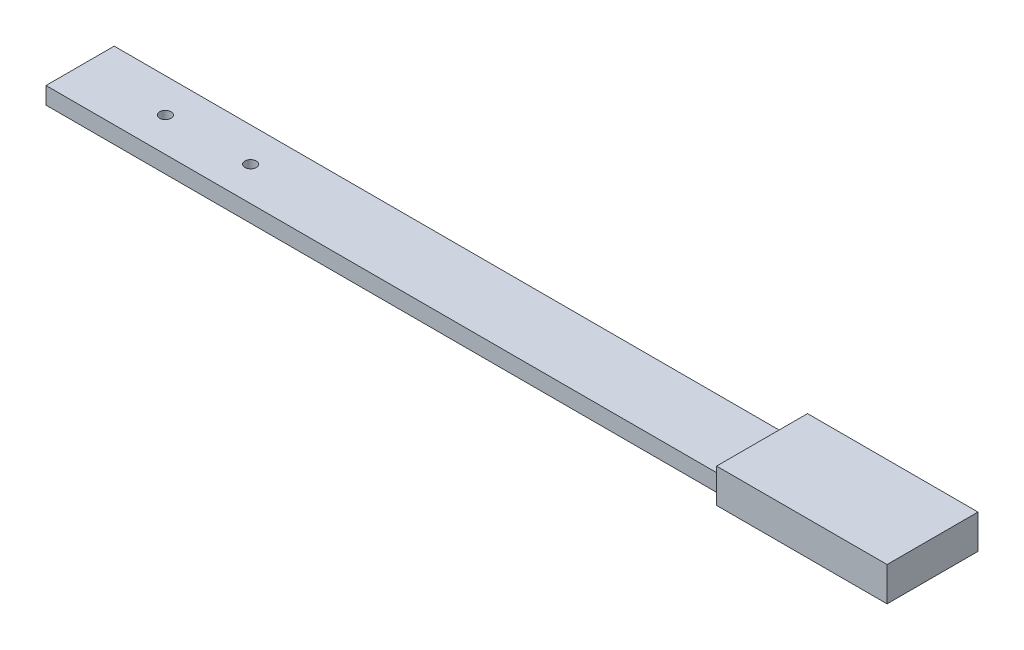
SolidWorks part; units mm, degrees
ref_plane "Ön Düzlem" through (0, 0, 0) normal (0, 0, 1) x (1, 0, 0)
ref_plane "Üst Düzlem" through (0, 0, 0) normal (0, 1, 0) x (1, 0, 0)
ref_plane "Sağ Düzlem" through (0, 0, 0) normal (1, 0, 0) x (0, 0, -1)
sketch "Çizim1" plane through (0, 0, 0) normal (0, 1, 0) x (1, 0, 0)
  line L1 (-375, -40) -> (375, -40)
  line L2 (-375, -40) -> (-375, 40)
  line L3 (-375, 40) -> (375, 40)
  line L4 (375, -40) -> (375, 40)
  line L5 (-375, -40) -> (375, 40) construction
  line L6 (-375, 40) -> (375, -40) construction
  circle A0 centre (-300, 0) radius 5
  circle A1 centre (-225, 0) radius 5
  circle A8 centre (225, 0) radius 5 [skipped]
  circle A9 centre (150, 0) radius 5 [skipped]
  circle A10 centre (75, 0) radius 5 [skipped]
  circle A11 centre (0, 0) radius 5 [skipped]
  circle A12 centre (-75, 0) radius 5 [skipped]
  circle A13 centre (-150, 0) radius 5 [skipped]
  point P0 (0, 0)
  dimension "D3" = 10
  dimension "D4" = 40
  dimension "D5" = 75
  dimension "D1" = 750
  dimension "D2" = 80
  dimension "D6" = 8
extrude "Yükseklik-Ekstrüzyon1" add sketch "Çizim1" against normal blind 30
sketch "Çizim3" plane through (-375, 0, 0) normal (-1, 0, 0) x (0, 0, 1)
  line L0 (-30, -30) -> (-30, -15)
  line L1 (-40, -30) -> (40, -30) construction
  line L2 (-30, -15) -> (30, -15)
  line L3 (30, -15) -> (30, -30)
  line L4 (30, -30) -> (40, -30)
  line L5 (40, -30) -> (40, 0)
  line L6 (40, 0) -> (-40, 0)
  line L7 (-40, 0) -> (40, 0) construction
  line L8 (-40, -30) -> (-40, 0) construction
  line L9 (-40, 0) -> (-40, -30)
  line L10 (-40, -30) -> (-30, -30)
  dimension "D1" = 15
  dimension "D2" = 10
  dimension "D3" = 10
extrude "Kes-Ekstrüzyon1" cut sketch "Çizim3" against normal blind 600
